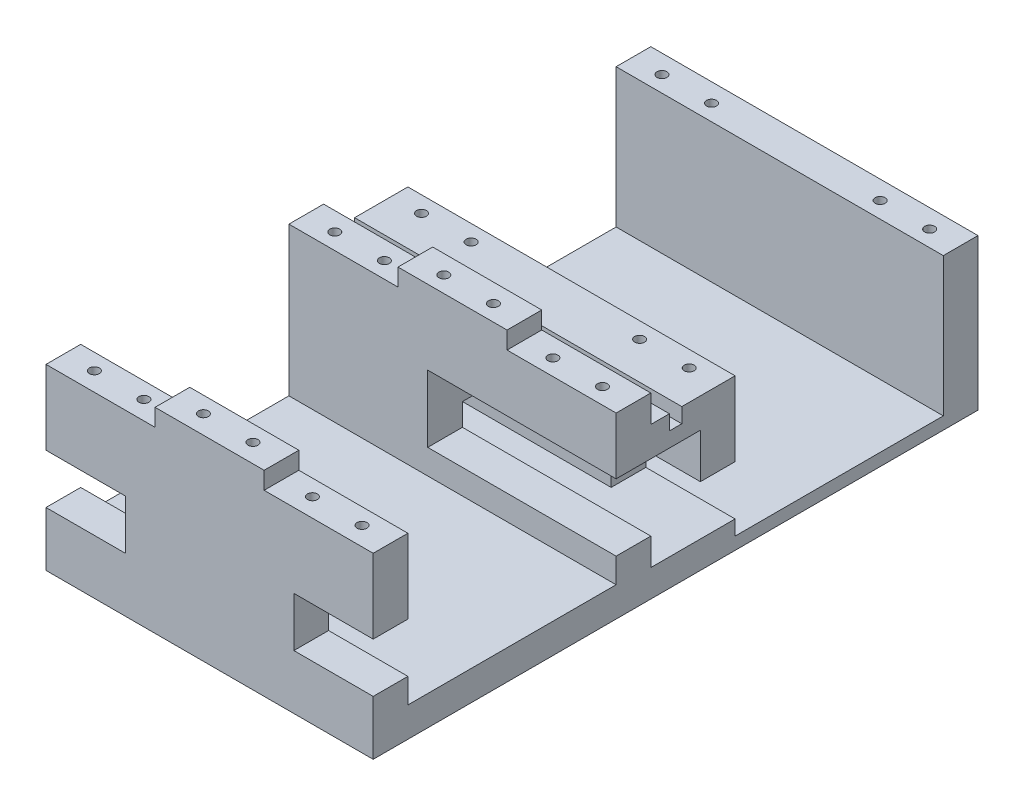
SolidWorks part; units mm, degrees
ref_plane "Front Plane" through (0, 0, 0) normal (0, 0, 1) x (1, 0, 0)
ref_plane "Top Plane" through (0, 0, 0) normal (0, 1, 0) x (1, 0, 0)
ref_plane "Right Plane" through (0, 0, 0) normal (1, 0, 0) x (0, 0, -1)
sketch "Sketch1" plane through (0, 0, 0) normal (0, 1, 0) x (1, 0, 0)
  line L1 (0, 0) -> (66, 0)
  line L2 (0, 0) -> (0, 56)
  line L3 (0, 56) -> (66, 56)
  line L4 (66, 0) -> (66, 56)
  dimension "D1" = 56
  dimension "D2" = 66
extrude "Boss-Extrude1" add sketch "Sketch1" along normal blind 6
sketch "Sketch2" plane through (0, 6, 0) normal (0, 1, 0) x (1, 0, 0)
  line L0 (66, 56) -> (0, 56) construction
  line L1 (0, 56) -> (66, 56)
  line L2 (0, 56) -> (0, 49)
  line L3 (0, 49) -> (66, 49)
  line L4 (66, 56) -> (66, 49)
  line L5 (66, 0) -> (66, 56) construction
  dimension "D1" = 7
extrude "Boss-Extrude2" add sketch "Sketch2" along normal blind 30
sketch "Sketch3" plane through (0, 6, 0) normal (0, 1, 0) x (1, 0, 0)
  line L0 (0, 49) -> (0, 0) construction
  line L1 (0, 28) -> (66, 28) construction
  line L2 (66, 0) -> (66, 49) construction
  line L3 (0, 0) -> (66, 0) construction
  line L4 (33, 0) -> (33, 114.9877) construction
  line L5 (11, 0) -> (11, 56) construction
  line L6 (66, 56) -> (0, 56) construction
  line L7 (55, 56) -> (55, 0) construction
  line L8 (0, 52.25) -> (66, 52.25) construction
  dimension "D1" = 28
  dimension "D2" = 33
  dimension "D3" = 11
  dimension "D4" = 11
  dimension "D5" = 24.25
sketch "Sketch4" plane through (0, 36, 0) normal (0, 1, 0) x (1, 0, 0)
  line L0 (66, 56) -> (0, 56) construction
  line L1 (22, 56) -> (44, 56)
  line L2 (22, 56) -> (22, 49)
  line L3 (22, 49) -> (44, 49)
  line L4 (44, 56) -> (44, 49)
  line L5 (0, 49) -> (66, 49) construction
  line L6 (0, 56) -> (0, 49) construction
  dimension "D1" = 22
  dimension "D2" = 22
extrude "Boss-Extrude3" add sketch "Sketch4" along normal blind 3.5
sketch "Sketch6" plane through (0, 36, 0) normal (0, 1, 0) x (1, 0, 0)
  line L0 (11, 0) -> (11, 56) construction
  line L1 (0, 52.25) -> (66, 52.25) construction
  line L2 (11, 56) -> (11, 49.0885) construction
  circle A0 centre (6, 52.25) radius 1
  circle A1 centre (16, 52.25) radius 1
  circle A2 centre (38, 52.25) radius 1
  circle A3 centre (28, 52.25) radius 1
  circle A4 centre (60, 52.25) radius 1
  circle A5 centre (50, 52.25) radius 1
  point P0 (11, 52.25)
  dimension "D1" = 2
  dimension "D2" = 5
  dimension "D3" = 3
extrude "Cut-Extrude1" cut sketch "Sketch6" against normal blind 10 and the other way blind 10
ref_plane "Plane1" through (0, 0, -28) normal (0, 0, 1) x (1, 0, 0)
mirror "Mirror1" about plane through (0, 0, -28) normal (0, 0, 1) of "Cut-Extrude1", "Boss-Extrude3", "Boss-Extrude2", "Boss-Extrude1"
sketch "Sketch15" plane through (0, 0, 0) normal (0, 1, 0) x (1, 0, 0)
  line L0 (66, 56) -> (0, 56) construction
  line L1 (0, 56) -> (66, 56)
  line L2 (0, 56) -> (0, 122)
  line L3 (0, 122) -> (66, 122)
  line L4 (66, 56) -> (66, 122)
  dimension "D1" = 66
extrude "Boss-Extrude4" add sketch "Sketch15" along normal blind 2.5
sketch "Sketch16" plane through (0, 2.5, 0) normal (0, 1, 0) x (1, 0, 0)
  line L0 (0, 122) -> (0, 56) construction
  line L1 (0, 66) -> (66, 66)
  line L2 (0, 66) -> (0, 73)
  line L3 (0, 73) -> (66, 73)
  line L4 (66, 66) -> (66, 73)
  line L5 (66, 56) -> (66, 122) construction
  line L6 (0, 56) -> (66, 56) construction
  dimension "D1" = 10
  dimension "D2" = 7
extrude "Boss-Extrude6" add sketch "Sketch16" along normal blind 28
sketch "Sketch17" plane through (0, 30.5, 0) normal (0, 1, 0) x (1, 0, 0)
  line L0 (33, 73) -> (33, 66) construction
  line L1 (66, 73) -> (0, 73) construction
  line L2 (0, 66) -> (66, 66) construction
  line L3 (11, 73) -> (11, 66) construction
  line L4 (0, 73) -> (0, 66) construction
  line L5 (0, 69.75) -> (66, 69.75) construction
  line L6 (66, 66) -> (66, 73) construction
  circle A0 centre (6, 69.75) radius 1
  circle A1 centre (16, 69.75) radius 1
  circle A2 centre (50, 69.75) radius 1
  circle A3 centre (60, 69.75) radius 1
  dimension "D3" = 2
  dimension "D1" = 11
  dimension "D2" = 3.25
  dimension "D4" = 5
extrude "Cut-Extrude2" cut sketch "Sketch17" against normal blind 10
sketch "Sketch18" plane through (0, 2.5, 0) normal (0, 1, 0) x (1, 0, 0)
  line L0 (0, 94) -> (66, 94) construction
  line L1 (0, 122) -> (0, 73) construction
  line L2 (66, 73) -> (66, 122) construction
  line L3 (66, 122) -> (0, 122) construction
  dimension "D1" = 28
ref_plane "Plane2" through (0, 0, -94) normal (0, 0, -1) x (-1, 0, 0)
mirror "Mirror2" about plane through (0, 0, -94) normal (0, 0, -1) of "Cut-Extrude2", "Boss-Extrude6"
sketch "Sketch14" plane through (0, 0, -7) normal (0, 0, -1) x (-1, 0, 0)
  line L1 (0, 11) -> (-16, 11)
  line L2 (0, 11) -> (0, 21)
  line L3 (0, 21) -> (-16, 21)
  line L4 (-16, 11) -> (-16, 21)
  line L5 (0, 36) -> (0, 6) construction
  line L6 (-22, 39.5) -> (-22, 36) construction
  line L7 (0, 6) -> (-66, 6) construction
  line L8 (-33, 6) -> (-33, 39.5) construction
  line L9 (-22, 39.5) -> (-44, 39.5) construction
  line L10 (-66, 21) -> (-50, 21)
  line L11 (-50, 11) -> (-50, 21)
  line L12 (-66, 11) -> (-50, 11)
  line L13 (-66, 11) -> (-66, 21)
  dimension "D1" = 0
  dimension "D2" = 6
  dimension "D3" = 5
  dimension "D4" = 10
sketch "Sketch19" plane through (0, 0, -73) normal (0, 0, -1) x (-1, 0, 0)
  line L0 (-18, 5.5) -> (0, 5.5)
  line L1 (-18, 5.5) -> (-18, 15.5)
  line L2 (-18, 15.5) -> (0, 15.5)
  line L3 (0, 5.5) -> (0, 15.5)
  line L4 (-33, 2.5) -> (-33, 35.9896) construction
  line L5 (-48, 15.5) -> (-66, 15.5)
  line L6 (-66, 5.5) -> (-66, 15.5)
  line L7 (-48, 5.5) -> (-66, 5.5)
  line L8 (-48, 5.5) -> (-48, 15.5)
  line L9 (-66, 2.5) -> (0, 2.5) construction
  line L10 (-66, 30.5) -> (-66, 2.5) construction
  point P18 (-33, 2.5)
  dimension "D1" = 3
  dimension "D2" = 10
  dimension "D3" = 15
extrude "Cut-Extrude3" cut sketch "Sketch14" against normal up to next
extrude "Cut-Extrude4" cut sketch "Sketch19" against normal up to next
sketch "Sketch24" plane through (0, 0, -66) normal (0, 0, 1) x (1, 0, 0)
  line L1 (0, 30.5) -> (66, 30.5)
  line L2 (0, 30.5) -> (0, 15.5)
  line L3 (0, 15.5) -> (66, 15.5)
  line L4 (66, 30.5) -> (66, 15.5)
extrude "Boss-Extrude9" add sketch "Sketch24" along normal blind 10
sketch "Sketch25" plane through (0, 0, -56) normal (0, 0, -1) x (-1, 0, 0)
  line L0 (-66, 15.5) -> (-66, 2.5) construction
  line L1 (-28, 7.5) -> (-66, 7.5)
  line L2 (-28, 7.5) -> (-28, 21)
  line L3 (-28, 21) -> (-66, 21)
  line L4 (-66, 7.5) -> (-66, 21)
  line L5 (0, 15.5) -> (0, 2.5) construction
  line L6 (0, 2.5) -> (-66, 2.5) construction
  dimension "D1" = 28
  dimension "D2" = 5
  dimension "D3" = 13.5
sketch "Sketch27" plane through (0, 0, -49) normal (0, 0, 1) x (1, 0, 0)
  line L0 (66, 36) -> (66, 6) construction
  line L1 (66, 11) -> (28, 11)
  line L2 (66, 11) -> (66, 24.5)
  line L3 (66, 24.5) -> (28, 24.5)
  line L4 (28, 11) -> (28, 24.5)
  line L6 (0, 6) -> (66, 6) construction
  line L7 (0, 36) -> (0, 6) construction
  dimension "D1" = 5
  dimension "D2" = 13.5
  dimension "D3" = 28
extrude "Cut-Extrude9" cut sketch "Sketch27" against normal blind 17
sketch "Sketch26" plane through (0, 0, -66) normal (0, 0, 1) x (1, 0, 0)
  line L1 (0, 5.5) -> (66, 5.5)
  line L2 (0, 5.5) -> (0, 2.5)
  line L3 (0, 2.5) -> (66, 2.5)
  line L4 (66, 5.5) -> (66, 2.5)
extrude "Boss-Extrude10" add sketch "Sketch26" along normal blind 10
sketch "Sketch28" plane through (0, 30.5, 0) normal (0, 1, 0) x (1, 0, 0)
  line L0 (0, 73) -> (0, 61) construction
  line L1 (0, 73) -> (0, 56) construction
  line L2 (0, 61) -> (66, 61) construction
  line L3 (66, 56) -> (66, 73) construction
  line L6 (0, 62.25) -> (66, 62.25)
  line L7 (0, 62.25) -> (0, 59.75)
  line L8 (0, 59.75) -> (66, 59.75)
  line L9 (66, 62.25) -> (66, 59.75)
  dimension "D1" = 12
  dimension "D2" = 1.25
  dimension "D3" = 1.25
extrude "Cut-Extrude10" cut sketch "Sketch28" against normal blind 3
